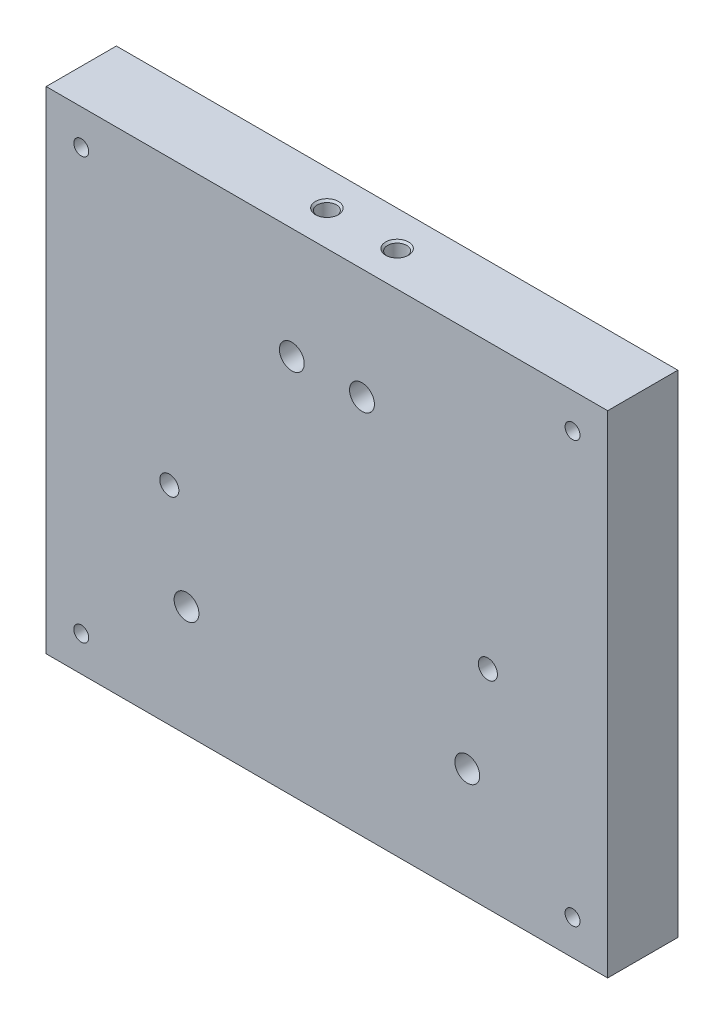
SolidWorks part; units mm, degrees
material "Brass"
ref_plane "Front Plane" through (0, 0, 0) normal (0, 0, 1) x (1, 0, 0)
ref_plane "Top Plane" through (0, 0, 0) normal (0, 1, 0) x (1, 0, 0)
ref_plane "Right Plane" through (0, 0, 0) normal (1, 0, 0) x (0, 0, -1)
sketch "Sketch1" plane through (0, 0, 0) normal (0, 0, 1) x (1, 0, 0)
  line L1 (0, 0) -> (-101.6, 0)
  line L2 (0, 0) -> (0, 88.9)
  line L3 (0, 88.9) -> (-101.6, 88.9)
  line L4 (-101.6, 0) -> (-101.6, 88.9)
  dimension "D1" = 101.6
  dimension "D2" = 88.9
extrude "Boss-Extrude1" add sketch "Sketch1" along normal blind 12.7
sketch "Sketch5" plane through (0, 88.9, 0) normal (0, 1, 0) x (1, 0, 0)
  line L0 (-101.6, -6.35) -> (0, -6.35) construction
  line L1 (-101.6, -12.7) -> (-101.6, 0) construction
  line L2 (0, -12.7) -> (0, 0) construction
  line L3 (-57.15, -6.35) -> (-44.45, -6.35)
  point P8 (-50.8, -6.35)
  dimension "D1" = 12.7
hole_wizard "#8-32 Tapped Hole1" positions "Sketch6" profile "Sketch8" tap size "#8-32" standard "ANSI Inch"
sketch "Sketch6" plane through (0, 88.9, 0) normal (0, 1, 0) x (1, 0, 0)
  point P0 (-44.45, -6.35)
  point P3 (-57.15, -6.35)
sketch "Sketch8" plane through (-44.45, 88.9, 6.35) normal (1, 0, 0) x (0, 0, 1)
  line L0 (0, 0) -> (0, 20.0878)
  line L1 (0, 20.0878) -> (1.7272, 19.05)
  line L2 (1.7272, 19.05) -> (1.7272, 0.3556)
  line L3 (1.7272, 0.3556) -> (2.0828, 0)
  line L5 (2.0828, 0) -> (0, 0)
  line L6 (-1.7272, 0.3556) -> (-2.0828, 0) construction
  line L10 (0, 20.0878) -> (-1.7272, 19.05) construction
  line L11 (0, -6.35) -> (0, 107.95) construction
  dimension "Tap Drill Dia." = 3.4544
  dimension "Tap Drill Depth" = 19.05
  dimension "Near C'Sink Dia." = 4.1656
  dimension "Near C'Sink Angle" = 90
  dimension "Drill Angle" = 118
cosmetic thread "Hole Thread1" parameters "D1"=12.7, "D2"=4.1656
cosmetic thread "Hole Thread2" parameters "D1"=12.7, "D2"=4.1656
hole_wizard "#8 Clearance Hole2" positions "Sketch11" profile "Sketch12" hole size "#8" standard "ANSI Inch"
sketch "Sketch11" plane through (0, 0, 12.7) normal (0, 0, 1) x (1, 0, 0)
  line L0 (-44.45, 68.8122) -> (-42.7228, 69.85) construction
  line L1 (-57.15, 68.8122) -> (-55.4228, 69.85) construction
  line L2 (-44.45, 68.8122) -> (-42.7228, 69.85)
  line L3 (-57.15, 68.8122) -> (-55.4228, 69.85)
  point P1 (-44.45, 68.8122)
  point P3 (-57.15, 68.8122)
sketch "Sketch12" plane through (-44.45, 68.8122, 12.7) normal (1, 0, 0) x (0, -1, 0)
  line L0 (0, 0) -> (0, 26.7507)
  line L1 (0, 26.7507) -> (2.2479, 25.4)
  line L2 (2.2479, 25.4) -> (2.2479, 0)
  line L5 (2.2479, 0) -> (0, 0)
  line L10 (0, 26.7507) -> (-2.2479, 25.4) construction
  line L11 (0, -6.35) -> (0, 107.95) construction
  dimension "Hole Dia." = 4.4958
  dimension "Hole Depth" = 25.4
  dimension "Drill Angle" = 118
sketch "Sketch13" plane through (0, 0, 12.7) normal (0, 0, 1) x (1, 0, 0)
  line L8 (-6.35, 6.35) -> (-6.35, 82.55)
  line L9 (-6.35, 82.55) -> (-95.25, 82.55)
  line L10 (-95.25, 82.55) -> (-95.25, 6.35)
  line L11 (-95.25, 6.35) -> (-6.35, 6.35)
  line L12 (-6.35, 6.35) -> (-6.35, 82.55)
  line L13 (-6.35, 82.55) -> (-95.25, 82.55)
  line L14 (-95.25, 82.55) -> (-95.25, 6.35)
  line L15 (-95.25, 6.35) -> (-6.35, 6.35)
  dimension "D1" = 6.35
hole_wizard "#6-32 Tapped Hole1" positions "Sketch14" profile "Sketch16" tap size "#6-32" standard "ANSI Inch" end condition through all
sketch "Sketch14" plane through (0, 0, 12.7) normal (0, 0, 1) x (1, 0, 0)
  point P0 (-95.25, 6.35)
  point P3 (-95.25, 82.55)
  point P6 (-6.35, 6.35)
  point P9 (-6.35, 82.55)
sketch "Sketch16" plane through (-95.25, 6.35, 12.7) normal (1, 0, 0) x (0, -1, 0)
  line L0 (0, 0) -> (0, 12.7)
  line L1 (0, 12.7) -> (1.3525, 12.7)
  line L2 (1.3525, 12.7) -> (1.3525, 0)
  line L5 (1.3525, 0) -> (0, 0)
  line L11 (0, -6.35) -> (0, 107.95) construction
  dimension "Thru Tap Drill Dia." = 2.7051
  dimension "Thru Tap Drill Depth" = 12.7
cosmetic thread "Hole Thread3" parameters "D2"=3.5052
cosmetic thread "Hole Thread4" parameters "D2"=3.5052
cosmetic thread "Hole Thread5" parameters "D2"=3.5052
cosmetic thread "Hole Thread6" parameters "D2"=3.5052
sketch "Sketch17" plane through (0, 0, 12.7) normal (0, 0, 1) x (1, 0, 0)
  line L0 (-82.55, 12.7) -> (-19.05, 12.7)
  line L1 (-82.55, 12.7) -> (-101.6, 12.7)
  line L2 (-101.6, 88.9) -> (-101.6, 0) construction
  line L3 (-19.05, 12.7) -> (0, 12.7)
  line L4 (0, 0) -> (0, 88.9) construction
  line L5 (-101.6, 0) -> (0, 0) construction
  dimension "D1" = 63.5
  dimension "D2" = 12.7
hole_wizard "#8-32 Tapped Hole2" positions "Sketch21" profile "Sketch22" tap size "#8-32" standard "ANSI Inch" end condition through all
sketch "Sketch21" plane through (0, 0, 0) normal (0, 0, -1) x (-1, 0, 0)
  line L9 (5.8, 8.89) -> (95.8, 8.89)
  line L10 (5.8, 66.294) -> (5.8, 8.89)
  line L11 (95.8, 66.294) -> (5.8, 66.294)
  line L12 (95.8, 8.89) -> (95.8, 66.294)
  line L13 (5.8, 8.89) -> (95.8, 8.89)
  line L14 (5.8, 66.294) -> (5.8, 8.89)
  line L15 (95.8, 66.294) -> (5.8, 66.294)
  line L16 (95.8, 8.89) -> (95.8, 66.294)
  circle A4 centre (21.675, 37.592) radius 2.2479
  circle A5 centre (21.675, 37.592) radius 2.2479
  circle A8 centre (79.3203, 37.592) radius 2.2479
  circle A9 centre (79.3203, 37.592) radius 2.2479
  point P53 (79.3203, 37.592)
  point P56 (21.675, 37.592)
  dimension "D1" = 0
  dimension "D2" = 0
  dimension "D3" = 0
sketch "Sketch22" plane through (-79.3203, 37.592, 0) normal (1, 0, 0) x (0, 1, 0)
  line L0 (0, 0) -> (0, 12.7)
  line L1 (0, 12.7) -> (1.7272, 12.7)
  line L2 (1.7272, 12.7) -> (1.7272, 0)
  line L5 (1.7272, 0) -> (0, 0)
  line L11 (0, -6.35) -> (0, 107.95) construction
  dimension "Thru Tap Drill Dia." = 3.4544
  dimension "Thru Tap Drill Depth" = 12.7
cosmetic thread "Hole Thread7" parameters "D2"=4.1656
cosmetic thread "Hole Thread8" parameters "D2"=4.1656
hole_wizard "#8-32 Tapped Hole3" positions "Sketch25" profile "Sketch26" tap size "#8-32" standard "ANSI Inch"
sketch "Sketch25" plane through (0, 0, 0) normal (0, -1, 0) x (-1, 0, 0)
  line L0 (76.2, -6.35) -> (25.4, -6.35)
  line L2 (0, -12.7) -> (0, 0) construction
  line L3 (101.6, -12.7) -> (101.6, 0) construction
  line L4 (76.2, -6.35) -> (101.6, -6.35) construction
  line L6 (25.4, -6.35) -> (0, -6.35) construction
  point P1 (76.2, -6.35)
  point P2 (25.4, -6.35)
  point P6 (0, -6.35)
  dimension "D1" = 50.8
sketch "Sketch26" plane through (-76.2, 0, 6.35) normal (1, 0, 0) x (0, 0, -1)
  line L0 (0, 0) -> (0, 20.0878)
  line L1 (0, 20.0878) -> (1.7272, 19.05)
  line L2 (1.7272, 19.05) -> (1.7272, 0)
  line L5 (1.7272, 0) -> (0, 0)
  line L10 (0, 20.0878) -> (-1.7272, 19.05) construction
  line L11 (0, -6.35) -> (0, 107.95) construction
  dimension "Tap Drill Dia." = 3.4544
  dimension "Tap Drill Depth" = 19.05
  dimension "Drill Angle" = 118
cosmetic thread "Hole Thread9" parameters "D1"=12.7, "D2"=4.1656
cosmetic thread "Hole Thread10" parameters "D1"=12.7, "D2"=4.1656
hole_wizard "#8 Clearance Hole3" positions "Sketch28" profile "Sketch29" hole size "#8" standard "ANSI Inch"
sketch "Sketch28" plane through (0, 0, 12.7) normal (0, 0, 1) x (1, 0, 0)
  line L0 (-74.4728, 19.05) -> (-76.2, 20.0878) construction
  line L1 (-74.4728, 19.05) -> (-76.2, 20.0878)
  line L2 (-76.2, 20.0878) -> (-77.9272, 19.05) construction
  line L3 (-76.2, 20.0878) -> (-77.9272, 19.05)
  line L4 (-25.4, 20.0878) -> (-27.1272, 19.05) construction
  line L5 (-23.6728, 19.05) -> (-25.4, 20.0878) construction
  line L6 (-25.4, 20.0878) -> (-27.1272, 19.05)
  line L7 (-23.6728, 19.05) -> (-25.4, 20.0878)
  point P2 (-76.2, 20.0878)
  point P5 (-25.4, 20.0878)
sketch "Sketch29" plane through (-76.2, 20.0878, 12.7) normal (1, 0, 0) x (0, -1, 0)
  line L0 (0, 0) -> (0, 20.4007)
  line L1 (0, 20.4007) -> (2.2479, 19.05)
  line L2 (2.2479, 19.05) -> (2.2479, 0)
  line L5 (2.2479, 0) -> (0, 0)
  line L10 (0, 20.4007) -> (-2.2479, 19.05) construction
  line L11 (0, -6.35) -> (0, 107.95) construction
  dimension "Hole Dia." = 4.4958
  dimension "Hole Depth" = 19.05
  dimension "Drill Angle" = 118
